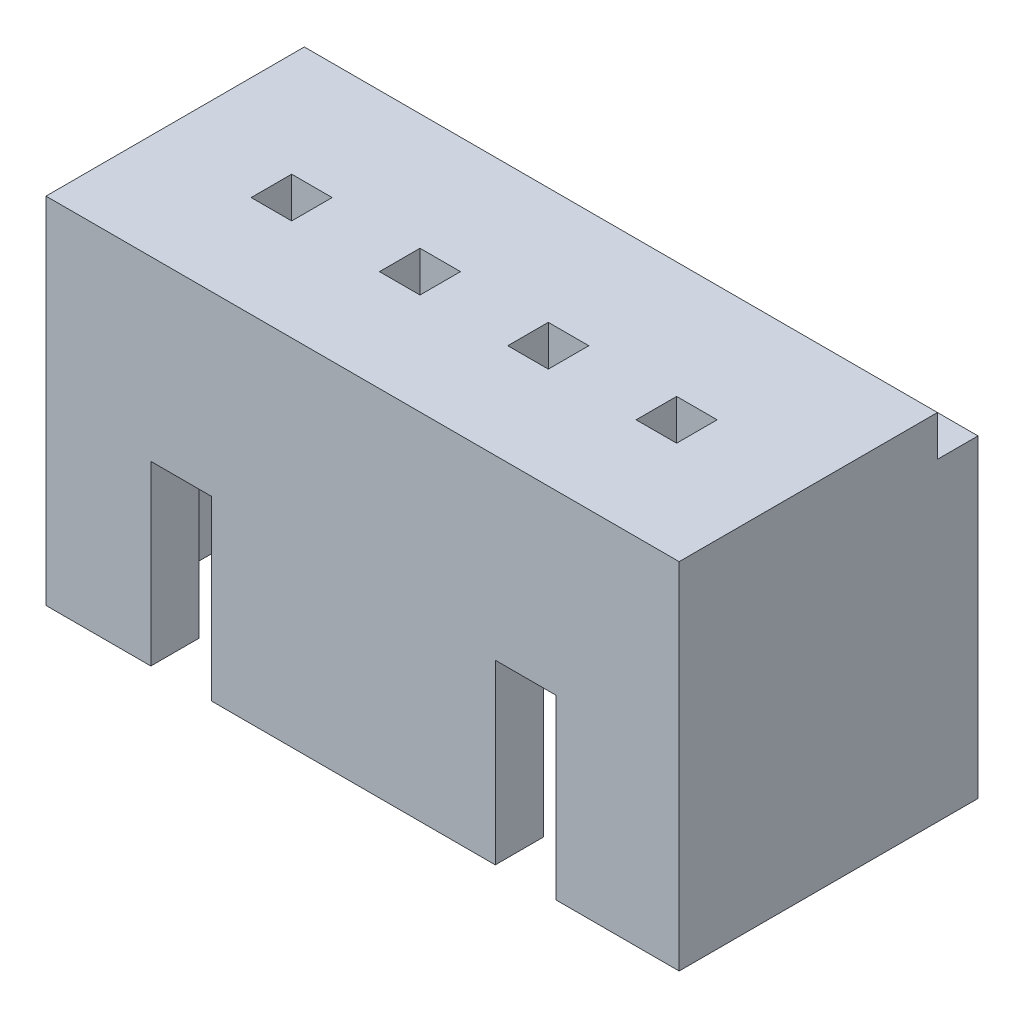
SolidWorks part; units mm, degrees
ref_plane "Front Plane" through (0, 0, 0) normal (0, 0, 1) x (1, 0, 0)
ref_plane "Top Plane" through (0, 0, 0) normal (0, 1, 0) x (1, 0, 0)
ref_plane "Right Plane" through (0, 0, 0) normal (1, 0, 0) x (0, 0, -1)
sketch "Sketch1" plane through (0, 0, 0) normal (0, 1, 0) x (1, 0, 0)
  line L1 (-6.25, -2.95) -> (6.25, -2.95)
  line L2 (-6.25, -2.95) -> (-6.25, 2.95)
  line L3 (-6.25, 2.95) -> (6.25, 2.95)
  line L4 (6.25, -2.95) -> (6.25, 2.95)
  line L5 (-6.25, -2.95) -> (6.25, 2.95) construction
  line L6 (-6.25, 2.95) -> (6.25, -2.95) construction
  point P0 (0, 0)
  dimension "D1" = 12.5
  dimension "D2" = 5.9
extrude "Boss-Extrude1" add sketch "Sketch1" along normal blind 7
sketch "Sketch3" plane through (0, 0, 0) normal (0, -1, 0) x (1, 0, 0)
  line L1 (-5.5, -2) -> (5.5, -2)
  line L2 (-5.5, -2) -> (-5.5, 2)
  line L3 (-5.5, 2) -> (5.5, 2)
  line L4 (5.5, -2) -> (5.5, 2)
  line L5 (-5.5, -2) -> (5.5, 2) construction
  line L6 (-5.5, 2) -> (5.5, -2) construction
  point P0 (0, 0)
  dimension "D1" = 11
  dimension "D2" = 4
extrude "Cut-Extrude1" cut sketch "Sketch3" against normal blind 5
sketch "Sketch4" plane through (0, 0, 2.95) normal (0, 0, 1) x (1, 0, 0)
  line L0 (-6.25, 0) -> (6.25, 0) construction
  line L1 (-4.18, 0) -> (-2.98, 0)
  line L2 (-4.18, 0) -> (-4.18, 3.5)
  line L3 (-4.18, 3.5) -> (-2.98, 3.5)
  line L4 (-2.98, 0) -> (-2.98, 3.5)
  line L6 (2.62, 0) -> (3.82, 0)
  line L7 (2.62, 0) -> (2.62, 3.5)
  line L8 (2.62, 3.5) -> (3.82, 3.5)
  line L9 (3.82, 0) -> (3.82, 3.5)
  dimension "D1" = 1.2
  dimension "D2" = 1.2
  dimension "D3" = 4.18
  dimension "D4" = 8
  dimension "D5" = 3.5
extrude "Cut-Extrude2" cut sketch "Sketch4" against normal blind 4
sketch "Sketch5" plane through (0, 7, 0) normal (0, 1, 0) x (1, 0, 0)
  line L0 (6.25, -2.95) -> (6.25, 2.95) construction
  line L1 (6.25, 2.15) -> (-6.25, 2.15)
  line L2 (6.25, 2.15) -> (6.25, 2.95)
  line L3 (6.25, 2.95) -> (-6.25, 2.95)
  line L4 (-6.25, 2.15) -> (-6.25, 2.95)
  dimension "D1" = 0.8
extrude "Cut-Extrude3" cut sketch "Sketch5" against normal blind 0.8 contours L1 L4 L3 L2
sketch "Sketch6" plane through (0, 7, 0) normal (0, 1, 0) x (1, 0, 0)
  line L0 (3.4, -0.15) -> (3.4, -0.95) construction
  line L1 (4.2, -0.95) -> (3.4, -0.95)
  line L2 (4.2, -0.95) -> (4.2, -0.15)
  line L3 (4.2, -0.15) -> (3.4, -0.15)
  line L4 (3.4, -0.95) -> (3.4, -0.15)
  line L5 (1.6667, -0.95) -> (1.6667, -0.15) construction
  line L6 (1.6667, -0.95) -> (0.8667, -0.95)
  line L7 (1.6667, -0.95) -> (1.6667, -0.15)
  line L8 (1.6667, -0.15) -> (0.8667, -0.15)
  line L9 (0.8667, -0.95) -> (0.8667, -0.15)
  line L10 (-0.8667, -0.15) -> (-1.6667, -0.15) construction
  line L11 (-0.8667, -0.95) -> (-1.6667, -0.95)
  line L12 (-0.8667, -0.95) -> (-0.8667, -0.15)
  line L13 (-0.8667, -0.15) -> (-1.6667, -0.15)
  line L14 (-1.6667, -0.95) -> (-1.6667, -0.15)
  line L16 (-3.4, -0.95) -> (-4.2, -0.95)
  line L17 (-3.4, -0.95) -> (-3.4, -0.15)
  line L18 (-3.4, -0.15) -> (-4.2, -0.15)
  line L19 (-4.2, -0.95) -> (-4.2, -0.15)
extrude "Cut-Extrude4" cut sketch "Sketch6" against normal blind 10
sketch "Sketch7" plane through (0, 5, 0) normal (0, -1, 0) x (1, 0, 0)
  line L0 (5.5, -2) -> (5.5, 2) construction
  line L1 (-5.5, -2) -> (5.5, -2)
  line L2 (-5.5, -2) -> (-5.5, -1)
  line L3 (-5.5, -1) -> (5.5, -1)
  line L4 (5.5, -2) -> (5.5, -1)
  dimension "D1" = 1
extrude "Cut-Extrude5" cut sketch "Sketch7" against normal blind 0.3
